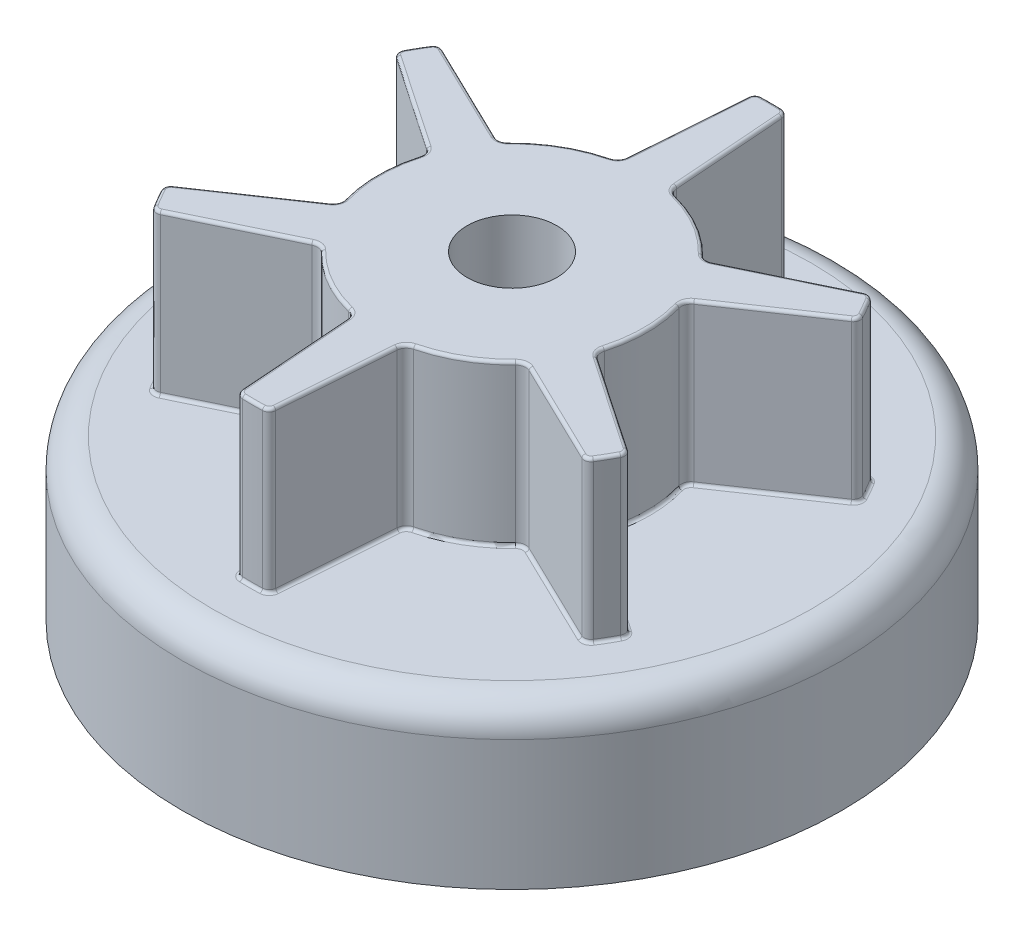
SolidWorks part; units mm, degrees
ref_plane "Front Plane" through (0, 0, 0) normal (0, 0, 1) x (1, 0, 0)
ref_plane "Top Plane" through (0, 0, 0) normal (0, 1, 0) x (1, 0, 0)
ref_plane "Right Plane" through (0, 0, 0) normal (1, 0, 0) x (0, 0, -1)
sketch "Sketch1" plane through (0, 0, 0) normal (0, 1, 0) x (1, 0, 0)
  circle A0 centre (0, 0) radius 33
  dimension "D1" = 66
extrude "Boss-Extrude1" add sketch "Sketch1" along normal blind 16
shell "Shell1" thickness 1.5
fillet "Fillet1" radius 3 2 edges at (0, 16, 33) (0, 14.5, 31.5)
sketch "Sketch2" plane through (0, 16, 0) normal (0, 1, 0) x (1, 0, 0)
  line L0 (0, 21.3312) -> (0, -25.0329) construction
  line L1 (1.6712, 25.3323) -> (2.5, 13.999)
  line L2 (-1.6712, 25.3323) -> (-2.5, 13.999)
  line L3 (-22.8779, 0) -> (22.9698, 0) construction
  line L4 (21.1028, 14.1135) -> (10.8735, 9.1646)
  line L5 (22.7741, 11.2189) -> (13.3735, 4.8344)
  line L6 (22.7741, -11.2189) -> (13.3735, -4.8344)
  line L7 (21.1028, -14.1135) -> (10.8735, -9.1646)
  line L8 (1.6712, -25.3323) -> (2.5, -13.999)
  line L9 (-1.6712, -25.3323) -> (-2.5, -13.999)
  line L10 (-21.1028, -14.1135) -> (-10.8735, -9.1646)
  line L11 (-22.7741, -11.2189) -> (-13.3735, -4.8344)
  line L12 (-22.7741, 11.2189) -> (-13.3735, 4.8344)
  line L13 (-21.1028, 14.1135) -> (-10.8735, 9.1646)
  arc A0 (1, 25.9808) -> (-1, 25.9808) centre (0, 0) ccw
  arc A1 (-3.2561, 13.1014) -> (-9.7181, 9.3706) centre (0, 0) ccw
  arc A2 (-2.5, 13.999) -> (-3.2561, 13.1014) centre (-3.4973, 14.0719) cw
  arc A3 (2.5, 13.999) -> (3.2561, 13.1014) centre (3.4973, 14.0719) ccw
  arc A4 (1.6712, 25.3323) -> (1, 25.9808) centre (0.9731, 25.2813) ccw
  arc A5 (-1.6712, 25.3323) -> (-1, 25.9808) centre (-0.9731, 25.2813) cw
  arc A6 (23, 12.1244) -> (22, 13.8564) centre (0, 0) ccw
  arc A7 (21.1028, 14.1135) -> (22, 13.8564) centre (21.4077, 13.4833) cw
  arc A8 (22.7741, 11.2189) -> (23, 12.1244) centre (22.3808, 11.7979) ccw
  arc A9 (13.3735, 4.8344) -> (12.9742, 3.7308) centre (13.9353, 4.0072) ccw
  arc A10 (10.8735, 9.1646) -> (9.7181, 9.3706) centre (10.438, 10.0647) cw
  arc A11 (22, -13.8564) -> (23, -12.1244) centre (0, 0) ccw
  arc A12 (22.7741, -11.2189) -> (23, -12.1244) centre (22.3808, -11.7979) cw
  arc A13 (21.1028, -14.1135) -> (22, -13.8564) centre (21.4077, -13.4833) ccw
  arc A14 (10.8735, -9.1646) -> (9.7181, -9.3706) centre (10.438, -10.0647) ccw
  arc A15 (13.3735, -4.8344) -> (12.9742, -3.7308) centre (13.9353, -4.0072) cw
  arc A16 (-1, -25.9808) -> (1, -25.9808) centre (0, 0) ccw
  arc A17 (1.6712, -25.3323) -> (1, -25.9808) centre (0.9731, -25.2813) cw
  arc A18 (-1.6712, -25.3323) -> (-1, -25.9808) centre (-0.9731, -25.2813) ccw
  arc A19 (-2.5, -13.999) -> (-3.2561, -13.1014) centre (-3.4973, -14.0719) ccw
  arc A20 (2.5, -13.999) -> (3.2561, -13.1014) centre (3.4973, -14.0719) cw
  arc A21 (-23, -12.1244) -> (-22, -13.8564) centre (0, 0) ccw
  arc A22 (-21.1028, -14.1135) -> (-22, -13.8564) centre (-21.4077, -13.4833) cw
  arc A23 (-22.7741, -11.2189) -> (-23, -12.1244) centre (-22.3808, -11.7979) ccw
  arc A24 (-13.3735, -4.8344) -> (-12.9742, -3.7308) centre (-13.9353, -4.0072) ccw
  arc A25 (-10.8735, -9.1646) -> (-9.7181, -9.3706) centre (-10.438, -10.0647) cw
  arc A26 (-22, 13.8564) -> (-23, 12.1244) centre (0, 0) ccw
  arc A27 (-22.7741, 11.2189) -> (-23, 12.1244) centre (-22.3808, 11.7979) cw
  arc A28 (-21.1028, 14.1135) -> (-22, 13.8564) centre (-21.4077, 13.4833) ccw
  arc A29 (-10.8735, 9.1646) -> (-9.7181, 9.3706) centre (-10.438, 10.0647) ccw
  arc A30 (-13.3735, 4.8344) -> (-12.9742, 3.7308) centre (-13.9353, 4.0072) cw
  arc A31 (-12.9742, 3.7308) -> (-12.9742, -3.7308) centre (0, 0) ccw
  arc A32 (-9.7181, -9.3706) -> (-3.2561, -13.1014) centre (0, 0) ccw
  arc A33 (3.2561, -13.1014) -> (9.7181, -9.3706) centre (0, 0) ccw
  arc A34 (12.9742, -3.7308) -> (12.9742, 3.7308) centre (0, 0) ccw
  arc A35 (9.7181, 9.3706) -> (3.2561, 13.1014) centre (0, 0) ccw
  point P10 (-2.5543, 13.2561)
  point P13 (2.5543, 13.2561)
  point P16 (1.6261, 25.9491)
  point P19 (-1.6261, 25.9491)
  point P85 (0, 0)
  dimension "D1" = 52
  dimension "D2" = 27
  dimension "D3" = 1
  dimension "D4" = 0.7
  dimension "D6" = 2
  dimension "D7" = 5
  dimension "D5" = 6
extrude "Boss-Extrude2" add sketch "Sketch2" along normal blind 16
fillet "Fillet2" radius 0.3 96 edges at (23.0599, 32, -11.6285) (18.0738, 32, -8.0266) (12.9949, 32, -4.3473) (13.5, 32, 0) (12.9949, 32, 4.3473) (18.0738, 32, 8.0266) (23.0599, 32, 11.6285) (22.5167, 32, 13) (21.6005, 32, 14.1563) (15.9882, 32, 11.639) (10.2624, 32, 9.0803) (6.75, 32, 11.6913) (2.7326, 32, 13.4276) (2.0856, 32, 19.6657) (1.4594, 32, 25.7847) (0, 32, 26) (-1.4594, 32, 25.7847) (-2.0856, 32, 19.6657) (-2.7326, 32, 13.4276) (-6.75, 32, 11.6913) (-10.2624, 32, 9.0803) (-15.9882, 32, 11.639) (-21.6005, 32, 14.1563) (-22.5167, 32, 13) (-23.0599, 32, 11.6285) (-18.0738, 32, 8.0266) (-12.9949, 32, 4.3473) (-13.5, 32, 0) (-12.9949, 32, -4.3473) (-18.0738, 32, -8.0266) (-23.0599, 32, -11.6285) (-22.5167, 32, -13) (-21.6005, 32, -14.1563) (-15.9882, 32, -11.639) (-10.2624, 32, -9.0803) (-6.75, 32, -11.6913) (-2.7326, 32, -13.4276) (-2.0856, 32, -19.6657) (-1.4594, 32, -25.7847) (0, 32, -26) (1.4594, 32, -25.7847) (2.0856, 32, -19.6657) (2.7326, 32, -13.4276) (6.75, 32, -11.6913) (10.2624, 32, -9.0803) (15.9882, 32, -11.639) (21.6005, 32, -14.1563) (21.6005, 16, -14.1563) (22.5167, 32, -13) (22.5167, 16, -13) (-2.7326, 16, 13.4276) (-23.0599, 16, 11.6285) (-21.6005, 16, 14.1563) (-10.2624, 16, 9.0803) (-12.9949, 16, 4.3473) (-12.9949, 16, -4.3473) (-23.0599, 16, -11.6285) (-22.5167, 16, -13) (-21.6005, 16, -14.1563) (-15.9882, 16, -11.639) (-10.2624, 16, -9.0803) (-6.75, 16, -11.6913) (-2.7326, 16, -13.4276) (-2.0856, 16, -19.6657) (-1.4594, 16, -25.7847) (0, 16, -26) (1.4594, 16, -25.7847) (2.0856, 16, -19.6657) (2.7326, 16, -13.4276) (6.75, 16, -11.6913) (10.2624, 16, -9.0803) (15.9882, 16, -11.639) (23.0599, 16, -11.6285) (18.0738, 16, -8.0266) (12.9949, 16, -4.3473) (13.5, 16, 0) (12.9949, 16, 4.3473) (18.0738, 16, 8.0266) (23.0599, 16, 11.6285) (21.6005, 16, 14.1563) (22.5167, 16, 13) (15.9882, 16, 11.639) (10.2624, 16, 9.0803) (2.7326, 16, 13.4276) (6.75, 16, 11.6913) (2.0856, 16, 19.6657) (1.4594, 16, 25.7847) (-1.4594, 16, 25.7847) (-2.0856, 16, 19.6657) (0, 16, 26) (-22.5167, 16, 13) (-15.9882, 16, 11.639) (-6.75, 16, 11.6913) (-18.0738, 16, 8.0266) (-18.0738, 16, -8.0266) (-13.5, 16, 0)
sketch "Sketch3" plane through (0, 14.5, 0) normal (0, -1, 0) x (1, 0, 0)
  circle A0 centre (0, 0) radius 4.5
  dimension "D1" = 9
extrude "Cut-Extrude1" cut sketch "Sketch3" against normal up to surface (17.5 mm away) up to face at (0, 32, 0)
sketch "Sketch4" plane through (0, 14.5, 0) normal (0, -1, 0) x (1, 0, 0)
  circle A0 centre (0, 0) radius 4.5 construction
  circle A1 centre (0, 0) radius 28.5
  circle A2 centre (0, 0) radius 28.5
  circle A3 centre (0, 0) radius 4.5
  circle A4 centre (0, 0) radius 5.5
  circle M3 centre (0, 0) radius 4.5
  dimension "D1" = 0
  dimension "D2" = 1
extrude "Boss-Extrude3" add sketch "Sketch4" along normal blind 2 contours A4 M3
fillet "Fillet3" radius 0.3 3 edges at (0, 12.5, -4.5) (0, 12.5, -5.5) (0, 14.5, 5.5)
